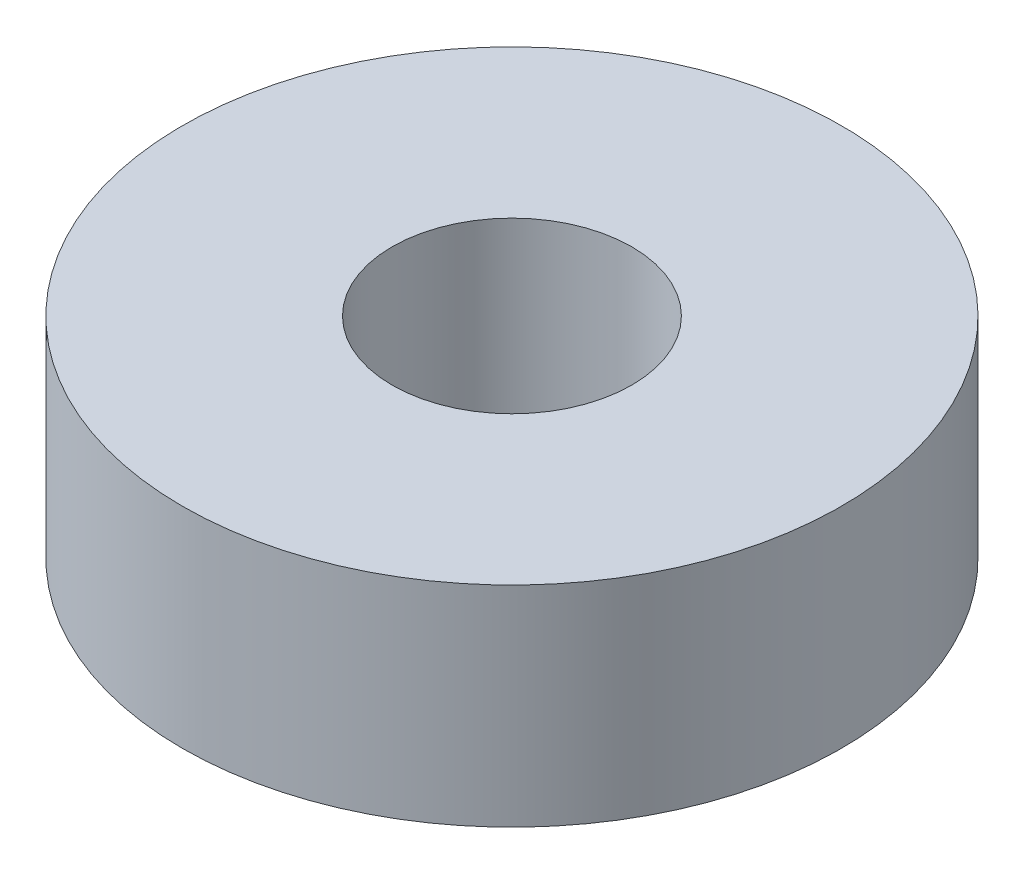
SolidWorks part; units mm, degrees
material "6061-T6 (SS)"
ref_plane "Front Plane" through (0, 0, 0) normal (0, 0, 1) x (1, 0, 0)
ref_plane "Top Plane" through (0, 0, 0) normal (0, 1, 0) x (1, 0, 0)
ref_plane "Right Plane" through (0, 0, 0) normal (1, 0, 0) x (0, 0, -1)
sketch "Sketch1" plane through (0, 0, 0) normal (0, 1, 0) x (1, 0, 0)
  circle A0 centre (0, 0) radius 11
  circle A1 centre (0, 0) radius 4
  dimension "D1" = 8
  dimension "D2" = 22
extrude "Boss-Extrude1" add sketch "Sketch1" along normal mid plane 7
